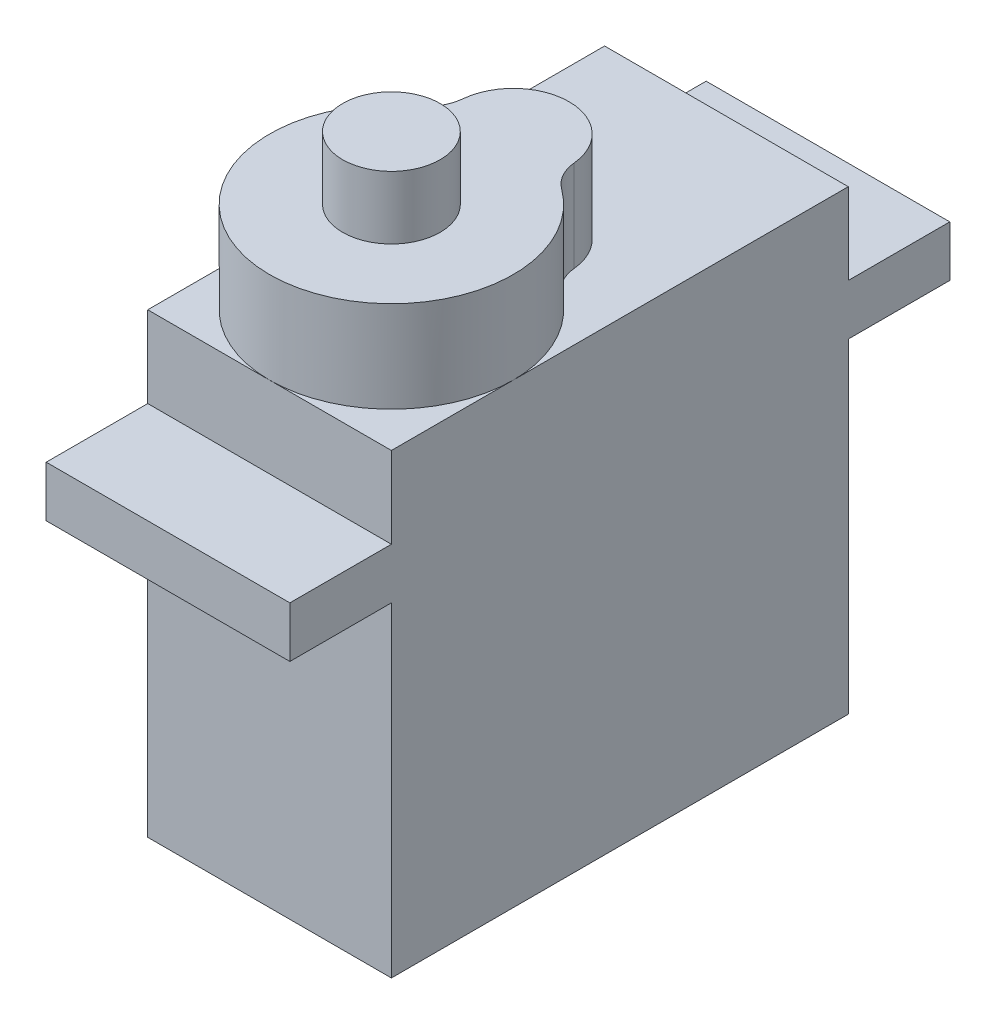
SolidWorks part; units mm, degrees
ref_plane "Alzado" through (0, 0, 0) normal (0, 0, 1) x (1, 0, 0)
ref_plane "Planta" through (0, 0, 0) normal (0, 1, 0) x (1, 0, 0)
ref_plane "Vista lateral" through (0, 0, 0) normal (1, 0, 0) x (0, 0, -1)
sketch "Croquis1" plane through (0, 0, 0) normal (0, 1, 0) x (1, 0, 0)
  line L1 (6, 11.25) -> (-6, 11.25)
  line L2 (6, 11.25) -> (6, -11.25)
  line L3 (6, -11.25) -> (-6, -11.25)
  line L4 (-6, 11.25) -> (-6, -11.25)
  line L5 (6, 11.25) -> (-6, -11.25) construction
  line L6 (6, -11.25) -> (-6, 11.25) construction
  point P0 (0, 0)
  dimension "D1" = 22.5
  dimension "D2" = 12
extrude "Saliente-Extruir1" add sketch "Croquis1" along normal blind 22.5
sketch "Croquis2" plane through (6, 0, 0) normal (1, 0, 0) x (0, 0, -1)
  line L0 (0, 22.5) -> (0, 18.5) construction
  line L1 (-11.25, 22.5) -> (11.25, 22.5) construction
  line L2 (-11.25, 18.5) -> (11.25, 18.5) construction
  line L3 (-11.25, 22.5) -> (-11.25, 0) construction
  line L4 (11.25, 22.5) -> (11.25, 0) construction
  line L5 (-11.25, 16) -> (11.25, 16) construction
  line L6 (-11.25, 18.5) -> (-16.25, 18.5)
  line L7 (-11.25, 18.5) -> (-11.25, 16)
  line L8 (-11.25, 16) -> (-16.25, 16)
  line L9 (-16.25, 18.5) -> (-16.25, 16)
  line L10 (11.25, 18.5) -> (16.25, 18.5)
  line L11 (11.25, 18.5) -> (11.25, 16)
  line L12 (11.25, 16) -> (16.25, 16)
  line L13 (16.25, 18.5) -> (16.25, 16)
  dimension "D1" = 2.5
  dimension "D2" = 4
  dimension "D3" = 5
  dimension "D4" = 5
extrude "Saliente-Extruir2" add sketch "Croquis2" against normal up to surface (12 mm away) up to face at (-6, 11.25, 0)
sketch "Croquis3" plane through (0, 22.5, 0) normal (0, 1, 0) x (1, 0, 0)
  line L0 (0, 11.25) -> (0, -5.25) construction
  line L1 (-6, 11.25) -> (6, 11.25) construction
  line L2 (-6, -11.25) -> (6, -11.25) construction
  circle A0 centre (0, -5.25) radius 6
  dimension "D2" = 12
  dimension "D3" = 6
  dimension "D1" = 16.5
extrude "Saliente-Extruir3" add sketch "Croquis3" along normal blind 4.5
sketch "Croquis4" plane through (0, 27, 0) normal (0, 1, 0) x (1, 0, 0)
  circle A0 centre (0, -5.25) radius 2.4
  dimension "D1" = 4.8
extrude "Saliente-Extruir4" add sketch "Croquis4" along normal blind 3.1
sketch "Croquis5" plane through (0, 22.5, 0) normal (0, 1, 0) x (1, 0, 0)
  circle A0 centre (0, 0.75) radius 2.75
  circle A1 centre (0, -5.25) radius 6 construction
  dimension "D1" = 6
  dimension "D2" = 5.5
extrude "Saliente-Extruir5" add sketch "Croquis5" along normal up to surface (4.5 mm away) up to face at (0, 27, 7.65)
fillet "Redondeo1" radius 2 2 edges at (2.6768, 24.75, -0.1198) (-2.6768, 24.75, -0.1198)
